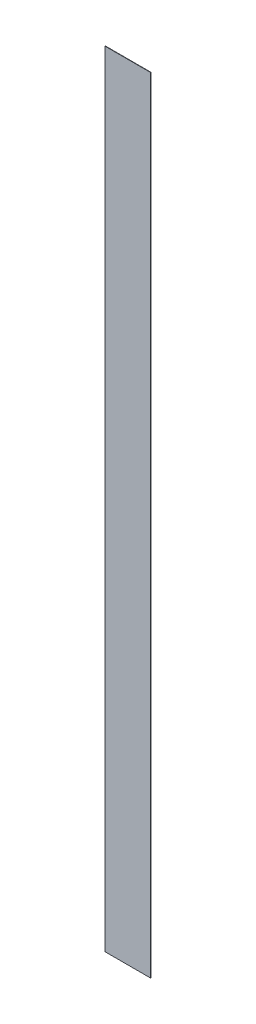
SolidWorks part; units mm, degrees
ref_plane "Front Plane" through (0, 0, 0) normal (0, 0, 1) x (1, 0, 0)
ref_plane "Top Plane" through (0, 0, 0) normal (0, 1, 0) x (1, 0, 0)
ref_plane "Right Plane" through (0, 0, 0) normal (1, 0, 0) x (0, 0, -1)
sketch "Sketch1" plane through (0, 0, 0) normal (0, 0, 1) x (1, 0, 0)
  line L0 (-10.9167, 37.002) -> (53.0833, 37.002) construction
  line L1 (-45.2253, 37.002) -> (-27.8735, 37.002)
  line L2 (-45.2253, 37.002) -> (-45.2253, 337.002)
  line L3 (-45.2253, 337.002) -> (-27.8735, 337.002)
  line L4 (-27.8735, 37.002) -> (-27.8735, 337.002)
  dimension "D1" = 300
extrude "Boss-Extrude1" add sketch "Sketch1" along normal blind 0.14
